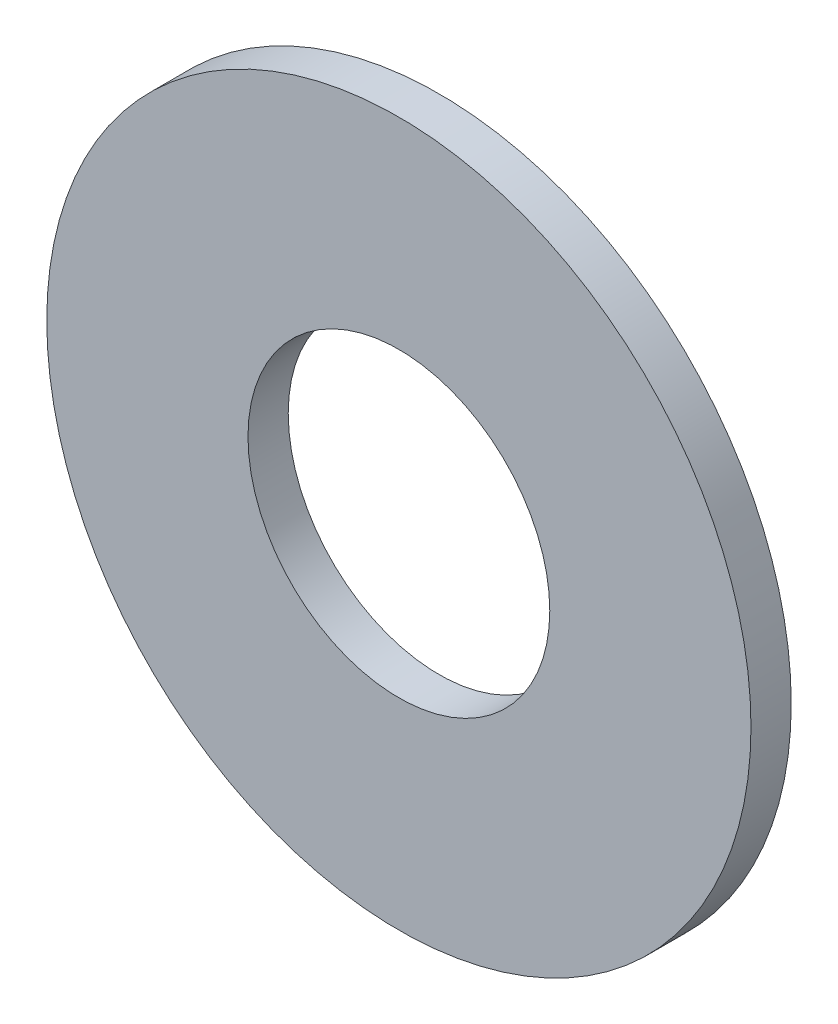
SolidWorks part; units mm, degrees
ref_plane "Front Plane" through (0, 0, 0) normal (0, 0, 1) x (1, 0, 0)
ref_plane "Top Plane" through (0, 0, 0) normal (0, 1, 0) x (1, 0, 0)
ref_plane "Right Plane" through (0, 0, 0) normal (1, 0, 0) x (0, 0, -1)
sketch "Sketch1" plane through (0, 0, 0) normal (0, 0, 1) x (1, 0, 0)
  circle A0 centre (0, 0) radius 17.5
  circle A1 centre (0, 0) radius 7.5
  dimension "D1" = 15
  dimension "D2" = 35
extrude "Boss-Extrude1" add sketch "Sketch1" along normal blind 2
